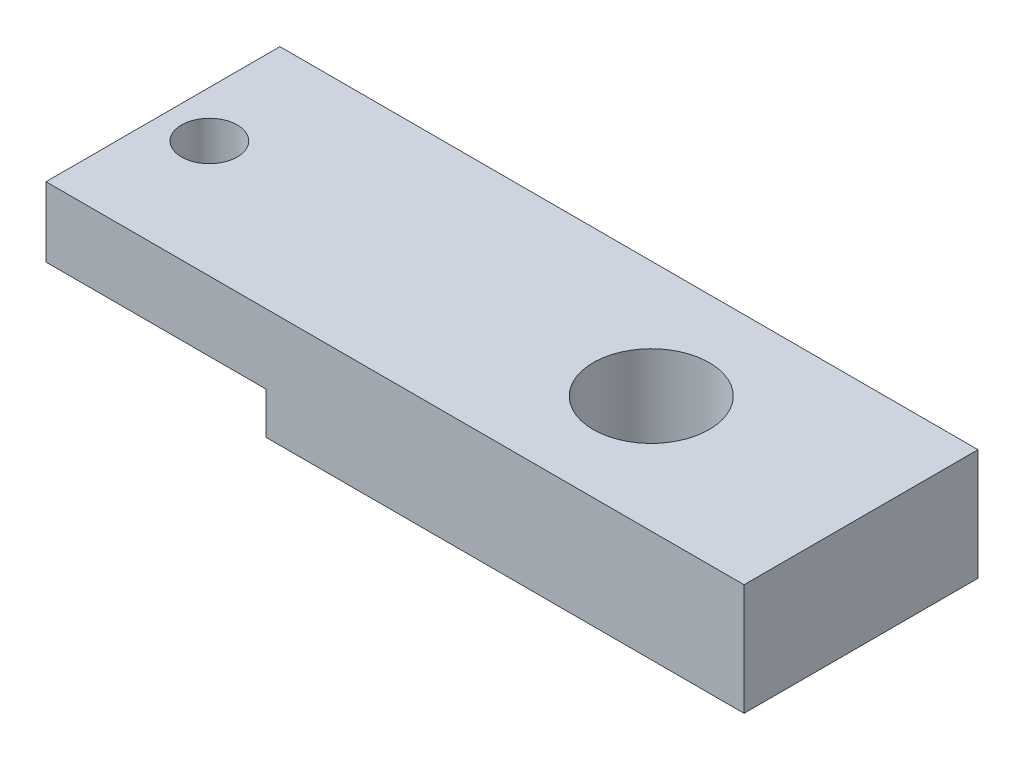
SolidWorks part; units mm, degrees
ref_plane "Front Plane" through (0, 0, 0) normal (0, 0, 1) x (1, 0, 0)
ref_plane "Top Plane" through (0, 0, 0) normal (0, 1, 0) x (1, 0, 0)
ref_plane "Right Plane" through (0, 0, 0) normal (1, 0, 0) x (0, 0, -1)
sketch "Sketch1" plane through (0, 0, 0) normal (0, 1, 0) x (1, 0, 0)
  line L1 (-9.5504, 3.2004) -> (9.5504, 3.2004)
  line L2 (-9.5504, 3.2004) -> (-9.5504, -3.2004)
  line L3 (-9.5504, -3.2004) -> (9.5504, -3.2004)
  line L4 (9.5504, 3.2004) -> (9.5504, -3.2004)
  line L5 (-9.5504, 3.2004) -> (9.5504, -3.2004) construction
  line L6 (-9.5504, -3.2004) -> (9.5504, 3.2004) construction
  point P0 (0, 0)
extrude "Boss-Extrude1" add sketch "Sketch1" along normal blind 1.905
sketch "Sketch2" plane through (0, 0, 0) normal (0, -1, 0) x (-1, 0, 0)
  line L0 (9.5504, -3.2004) -> (-9.5504, -3.2004) construction
  line L1 (-9.5504, 3.2004) -> (3.5306, 3.2004)
  line L2 (-9.5504, 3.2004) -> (-9.5504, -3.2004)
  line L3 (-9.5504, -3.2004) -> (3.5306, -3.2004)
  line L4 (3.5306, 3.2004) -> (3.5306, -3.2004)
extrude "Boss-Extrude2" add sketch "Sketch2" along normal blind 1.143
sketch "Sketch3" plane through (0, 1.905, 0) normal (0, 1, 0) x (1, 0, 0)
  circle A0 centre (-8.2804, 0) radius 0.762
  point P2 (0, 0)
  point P3 (0, 0)
  point P6 (0, 0)
  point P7 (0, 0)
extrude "Cut-Extrude1" cut sketch "Sketch3" against normal up to next
sketch "Sketch4" plane through (0, 1.905, 0) normal (0, 1, 0) x (1, 0, 0)
  circle A0 centre (3.81, 0) radius 1.5875
extrude "Cut-Extrude2" cut sketch "Sketch4" against normal up to next
